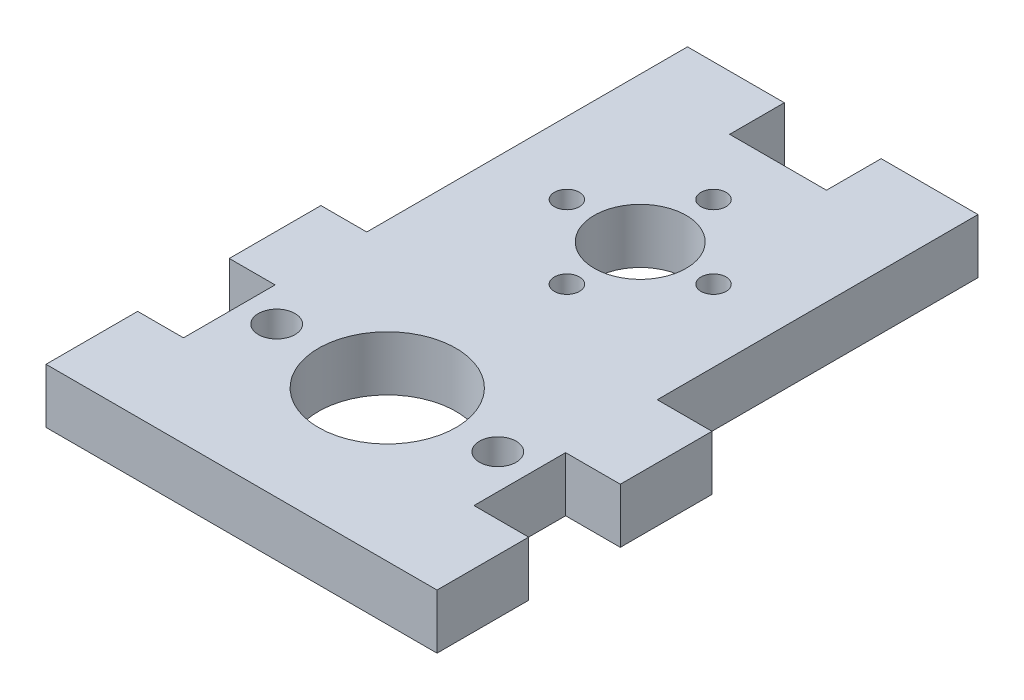
SolidWorks part; units mm, degrees
ref_plane "Front Plane" through (0, 0, 0) normal (0, 0, 1) x (1, 0, 0)
ref_plane "Top Plane" through (0, 0, 0) normal (0, 1, 0) x (1, 0, 0)
ref_plane "Right Plane" through (0, 0, 0) normal (1, 0, 0) x (0, 0, -1)
sketch "Sketch1" plane through (0, 0, 0) normal (0, 1, 0) x (1, 0, 0)
  line L0 (0, 55) -> (31.7, 55) construction
  line L1 (0, 0) -> (31.7, 0)
  line L2 (0, 0) -> (0, 65)
  line L3 (0, 65) -> (10.5667, 65)
  line L4 (31.7, 0) -> (31.7, 65)
  line L5 (15.85, 65) -> (15.85, 0) construction
  line L6 (21.1333, 65) -> (31.7, 65)
  line L8 (21.1333, 65) -> (21.1333, 59.031)
  line L9 (21.1333, 59.031) -> (10.5667, 59.031)
  line L10 (10.5667, 65) -> (10.5667, 59.031)
  line L11 (10.5667, 65) -> (21.1333, 65) construction
  circle A0 centre (15.85, 43.99) radius 5.015
  circle A1 centre (15.85, 43.99) radius 11.01 construction
  circle A2 centre (15.85, 16.3861) radius 7.5
  dimension "D4" = 10.03
  dimension "D5" = 22.02
  dimension "D7" = 15
  dimension "D1" = 65
  dimension "D2" = 31.7
  dimension "D3" = 10
  dimension "D6" = 27.6039
  dimension "D8" = 5.969
extrude "Boss-Extrude1" add sketch "Sketch1" along normal blind 5.969
sketch "Sketch2" plane through (0, 5.969, 0) normal (0, 1, 0) x (1, 0, 0)
  line L5 (0, 65) -> (0, 0) construction
  line L12 (0, 0) -> (-5, 0)
  line L17 (0, 0) -> (0, 10)
  line L18 (0, 10) -> (-5, 10)
  line L24 (-5, 0) -> (-5, 10)
  line L26 (0, 20) -> (-5, 20)
  line L27 (0, 20) -> (0, 30)
  line L32 (0, 30) -> (-5, 30)
  line L35 (-5, 20) -> (-5, 30)
  line L36 (0, 20) -> (-5, 30) construction
  line L37 (0, 30) -> (-5, 20) construction
  line L38 (15.85, 0) -> (15.85, 59.031) construction
  line L39 (0, 0) -> (31.7, 0) construction
  line L40 (21.1333, 59.031) -> (10.5667, 59.031) construction
  line L43 (37.669, 20) -> (37.669, 30)
  line L44 (31.7, 30) -> (37.669, 30)
  line L45 (31.7, 20) -> (31.7, 30)
  line L46 (31.7, 20) -> (37.669, 20)
  line L47 (37.669, 0) -> (37.669, 10)
  line L48 (31.7, 10) -> (37.669, 10)
  line L49 (31.7, 0) -> (31.7, 10)
  line L50 (31.7, 0) -> (37.669, 0)
  point P8 (-2.5, 25)
  dimension "D1" = 5
  dimension "D2" = 10
  dimension "D3" = 10
  dimension "D4" = 5.969
extrude "Boss-Extrude2" add sketch "Sketch2" against normal blind 5.969
sketch "Sketch3" plane through (0, 0, 0) normal (0, -1, 0) x (1, 0, 0)
  line L0 (8.35, -16.3861) -> (23.35, -16.3861) construction
  line L1 (15.85, -8.8861) -> (15.85, -23.8861) construction
  line L2 (15.85, -16.3861) -> (27.915, -16.3861) construction
  line L3 (15.85, -16.3861) -> (3.785, -16.3861) construction
  circle A0 centre (15.85, -16.3861) radius 7.5 construction
  circle A1 centre (27.915, -16.3861) radius 2
  circle A2 centre (3.785, -16.3861) radius 2
  dimension "D2" = 4
  dimension "D1" = 24.13
extrude "Cut-Extrude1" cut sketch "Sketch3" against normal through all
sketch "Sketch4" plane through (0, 0, 0) normal (0, -1, 0) x (1, 0, 0)
  line L1 (15.85, -38.975) -> (15.85, -49.005) construction
  line L2 (7.85, -43.99) -> (10.835, -43.99) construction
  line L3 (10.835, -43.99) -> (20.865, -43.99) construction
  line L4 (20.865, -43.99) -> (23.85, -43.99) construction
  line L5 (15.85, -38.975) -> (15.85, -35.99) construction
  line L6 (15.85, -51.99) -> (15.85, -49.005) construction
  circle A0 centre (15.85, -43.99) radius 5.015 construction
  circle A1 centre (23.85, -43.99) radius 1.37
  circle A2 centre (15.85, -51.99) radius 1.37
  circle A3 centre (15.85, -35.99) radius 1.37
  circle A4 centre (7.85, -43.99) radius 1.37
  dimension "D1" = 2.74
  dimension "D2" = 16
  dimension "D3" = 16
extrude "Cut-Extrude2" cut sketch "Sketch4" against normal through all
